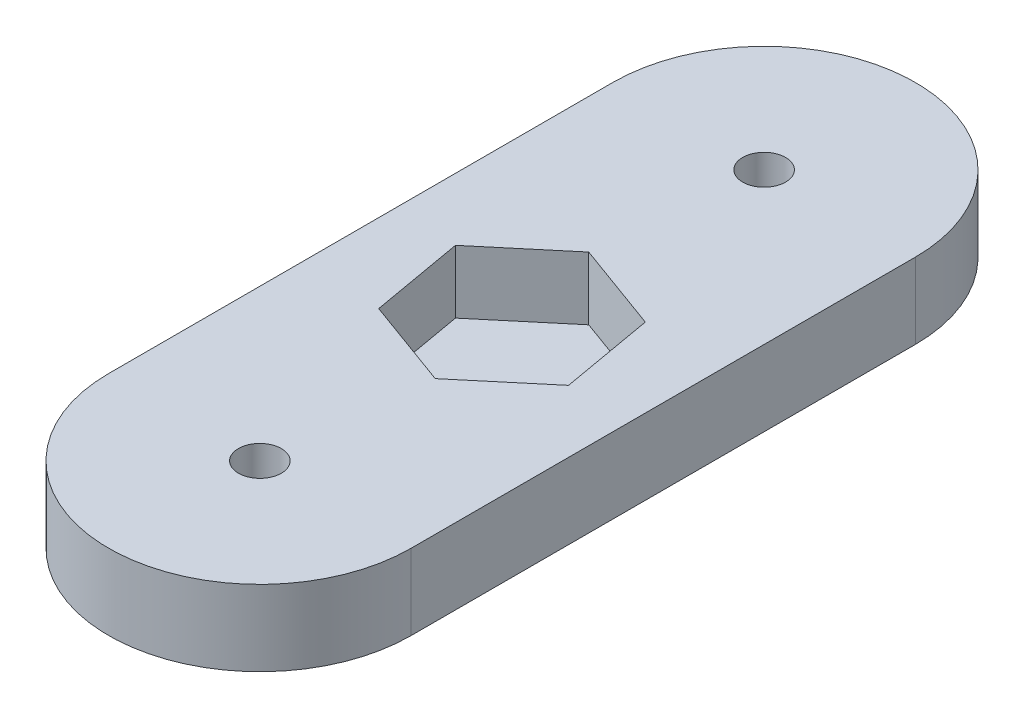
SolidWorks part; units mm, degrees
material "ABS PC"
ref_plane "Front Plane" through (0, 0, 0) normal (0, 0, 1) x (1, 0, 0)
ref_plane "Top Plane" through (0, 0, 0) normal (0, 1, 0) x (1, 0, 0)
ref_plane "Right Plane" through (0, 0, 0) normal (1, 0, 0) x (0, 0, -1)
sketch "Sketch1" plane through (0, 0, 0) normal (0, 1, 0) x (1, 0, 0)
  line L0 (0, 0) -> (0, 40) construction
  line L1 (-12, 0) -> (-12, 40)
  line L2 (12, 0) -> (12, 40)
  arc A0 (-12, 0) -> (12, 0) centre (0, 0) ccw
  arc A1 (12, 40) -> (-12, 40) centre (0, 40) ccw
  circle A2 centre (0, 40) radius 1.7
  circle A3 centre (0, 0) radius 1.7
  point P3 (0, 20)
  dimension "D2" = 40
  dimension "D3" = 3.4
  dimension "D1" = 24
extrude "Boss-Extrude1" add sketch "Sketch1" along normal blind 6
sketch "Sketch2" plane through (0, 6, 0) normal (0, 1, 0) x (1, 0, 0)
  line L0 (12, 0) -> (12, 40) construction
  line L1 (1.3033, 12.6085) -> (7.0529, 17.4329)
  line L2 (7.0529, 17.4329) -> (5.7496, 24.8245)
  line L3 (5.7496, 24.8245) -> (-1.3033, 27.3915)
  line L4 (-1.3033, 27.3915) -> (-7.0529, 22.5671)
  line L5 (-7.0529, 22.5671) -> (-5.7496, 15.1755)
  line L6 (-5.7496, 15.1755) -> (1.3033, 12.6085)
  line L7 (-12, 40) -> (-12, 0) construction
  circle A0 centre (0, 20) radius 6.5 construction
  dimension "D1" = 13
  dimension "D2" = 12
  dimension "D3" = 20
  dimension "D4" = 70
extrude "Cut-Extrude1" cut sketch "Sketch2" against normal blind 5
